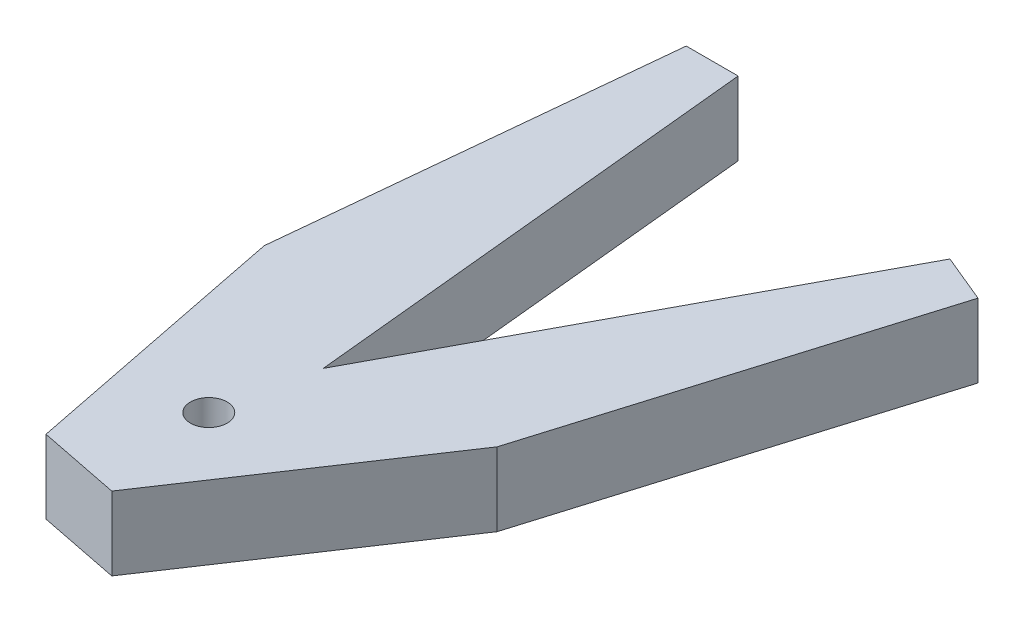
SolidWorks part; units mm, degrees
ref_plane "Face" through (0, 0, 0) normal (0, 0, 1) x (1, 0, 0)
ref_plane "Dessus" through (0, 0, 0) normal (0, 1, 0) x (1, 0, 0)
ref_plane "Droite" through (0, 0, 0) normal (1, 0, 0) x (0, 0, -1)
sketch "Esquisse1" plane through (0, 0, 0) normal (0, 1, 0) x (1, 0, 0)
  line L0 (-190, 0) -> (190, 0) construction
  line L1 (0, 0) -> (134.3503, 134.3503) construction
  line L2 (0, -190) -> (0, 190) construction
  line L3 (-21.6828, 82.3523) -> (-16.5827, 83.3667) construction
  line L4 (134.3503, -134.3503) -> (-134.3503, 134.3503) construction
  line L5 (72.6736, 175.4496) -> (0, 0) construction
  line L6 (-134.3503, -134.3503) -> (0, 0) construction
  line L7 (0, 190) -> (72.6736, 175.4496) construction
  line L8 (-6, 189.9052) -> (0, 189.9052)
  line L9 (0, 189.9052) -> (6, 189.9052)
  line L10 (6, 189.9052) -> (16.5827, 83.3667)
  line L11 (67.1303, 177.7457) -> (72.6736, 175.4496)
  line L12 (72.6736, 175.4496) -> (78.2169, 173.1535)
  line L13 (16.5827, 83.3667) -> (67.1303, 177.7457)
  line L14 (47.2235, 70.6749) -> (78.2169, 173.1535) construction
  line L15 (-16.5827, 83.3667) -> (-6, 189.9052) construction
  line L16 (-16.5827, 83.3667) -> (0, 0) construction
  line L17 (0, 0) -> (47.2235, 70.6749) construction
  line L18 (-16.5827, 83.3667) -> (-7.8036, 39.2314) construction
  line L19 (-2.2833, 38.1334) -> (16.7025, 34.3568)
  line L20 (-11.4826, 84.3812) -> (-14.8169, 101.1437)
  line L21 (-12.6809, 63.751) -> (-7.8036, 39.2314) construction
  line L22 (42.8998, 73.5639) -> (52.395, 87.7744)
  line L23 (0, 0) -> (66.4089, 333.8601)
  line L24 (-16.5827, 83.3667) -> (-11.4826, 84.3812) construction
  line L25 (-11.4826, 84.3812) -> (-7.5808, 64.7655)
  line L26 (-7.5808, 64.7655) -> (-12.4027, 63.8064) construction
  line L27 (-12.6809, 63.751) -> (-17.781, 62.7366) construction
  line L28 (-17.781, 62.7366) -> (-21.6828, 82.3523) construction
  line L29 (47.2235, 70.6749) -> (42.8998, 73.5639) construction
  line L30 (42.8998, 73.5639) -> (31.7884, 56.9345)
  line L31 (36.1121, 54.0455) -> (22.2228, 33.2588) construction
  line L32 (31.7884, 56.9345) -> (35.8762, 54.2031) construction
  line L33 (-6, 189.9052) -> (-14.8169, 101.1437)
  line L34 (78.2169, 173.1535) -> (52.395, 87.7744)
  line L35 (0, 0) -> (68.072, 102.8456) construction
  line L36 (35.8762, 54.2031) -> (22.0379, 33.2956) construction
  line L37 (-12.4027, 63.8064) -> (-7.6187, 39.1946) construction
  line L38 (-7.5808, 64.7655) -> (-2.2833, 38.1334)
  line L39 (31.7884, 56.9345) -> (16.7025, 34.3568)
  circle A0 centre (0, 0) radius 190 construction
  circle A1 centre (0, 0) radius 85 construction
  circle A2 centre (0, 0) radius 40 construction
  circle A3 centre (0, 0) radius 62.5 construction
  circle A4 centre (12.1931, 61.2991) radius 4.25
  point P27 (0, 0)
  point P29 (-0.0761, -1.5101)
  point P30 (0, 0)
  dimension "D1" = 380
  dimension "D2" = 170
  dimension "D3" = 80
  dimension "D8" = 11
  dimension "D6" = 125
  dimension "D14" = 8.5
  dimension "D4" = 6
  dimension "D5" = 2
  dimension "D9" = 22.5
  dimension "D10" = 45
  dimension "D11" = 11.25
  dimension "D12" = 20
  dimension "D13" = 5.2
  dimension "D7" = 2
extrude "Boss.-Extru.1" add sketch "Esquisse1" along normal blind 17
ref_plane "Plan1" through (0, 0, 0) normal (0.9808, 0, 0.1951) x (0, -1, 0)
sketch "Encombrement" plane through (0, 17, 0) normal (0, 1, 0) x (1, 0, 0)
  line L0 (-5.5433, 192.2013) -> (-34.8988, 44.621)
  line L1 (-34.8988, 44.621) -> (49.318, 27.8692)
  line L2 (49.318, 27.8692) -> (78.6736, 175.4496)
  line L3 (78.6736, 175.4496) -> (-5.5433, 192.2013)
  dimension "D1" = 150.4716
  dimension "D2" = 85.8668
